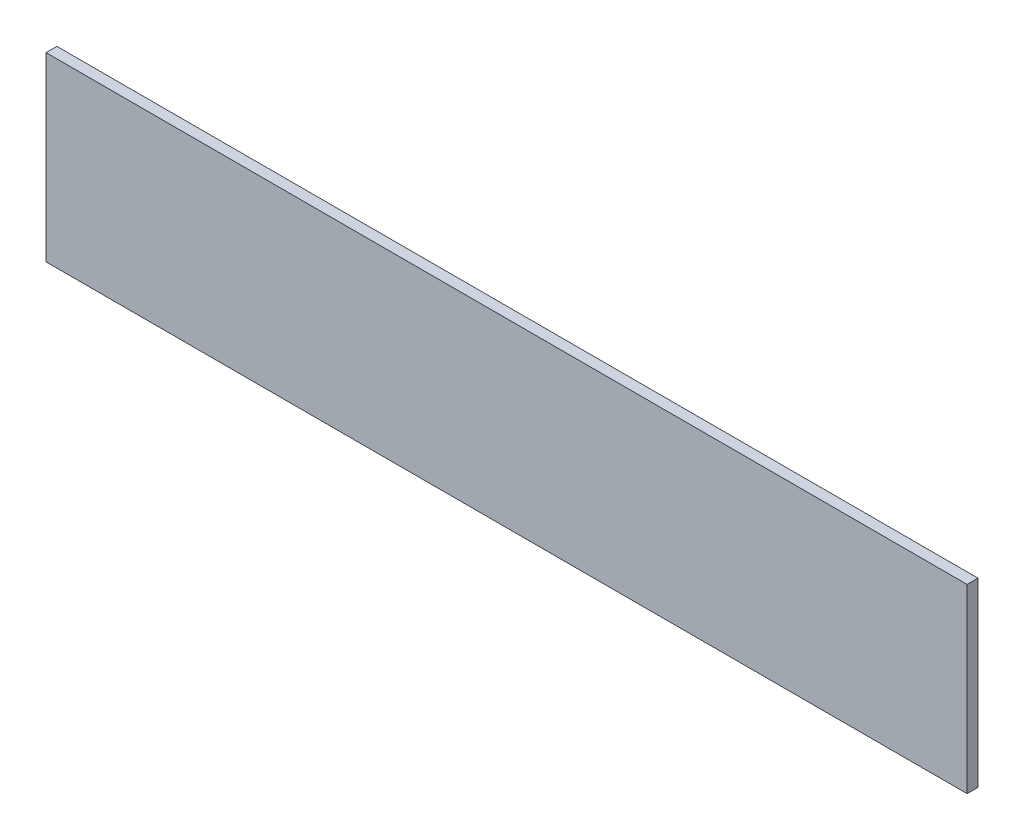
SolidWorks part; units mm, degrees
ref_plane "Ebene vorne" through (0, 0, 0) normal (0, 0, 1) x (1, 0, 0)
ref_plane "Ebene oben" through (0, 0, 0) normal (0, 1, 0) x (1, 0, 0)
ref_plane "Ebene rechts" through (0, 0, 0) normal (1, 0, 0) x (0, 0, -1)
sketch "Skizze1" plane through (0, 0, 0) normal (0, 0, 1) x (1, 0, 0)
  line L1 (-762.5, 150) -> (762.5, 150)
  line L2 (-762.5, 150) -> (-762.5, -150)
  line L3 (-762.5, -150) -> (762.5, -150)
  line L4 (762.5, 150) -> (762.5, -150)
  line L5 (-762.5, 150) -> (762.5, -150) construction
  line L6 (-762.5, -150) -> (762.5, 150) construction
  point P0 (0, 0)
  dimension "D1" = 300
  dimension "D2" = 1525
extrude "Aufsatz-Linear austragen1" add sketch "Skizze1" along normal blind 18
